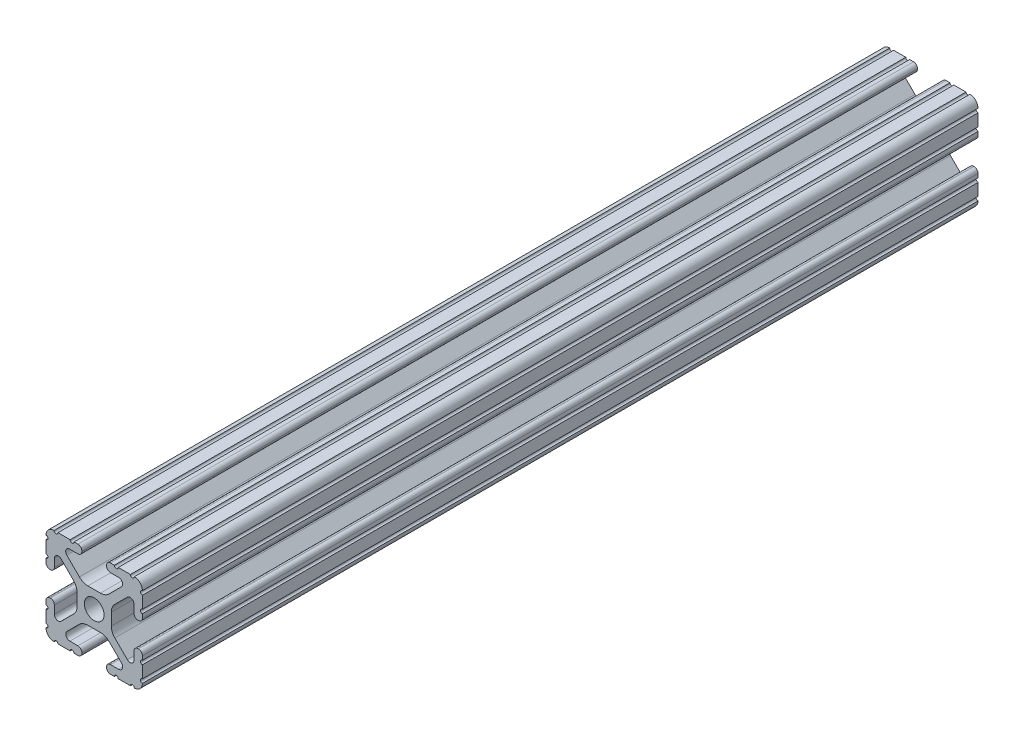
SolidWorks part; units mm, degrees
ref_plane "Front Plane" through (0, 0, 0) normal (0, 0, 1) x (1, 0, 0)
ref_plane "Top Plane" through (0, 0, 0) normal (0, 1, 0) x (1, 0, 0)
ref_plane "Right Plane" through (0, 0, 0) normal (1, 0, 0) x (0, 0, -1)
sketch "Sketch1" plane through (0, 0, 0) normal (0, 0, 1) x (1, 0, 0)
  line L88 (-7.1797, -8.6452) -> (-3.9523, -5.4237)
  line L89 (-1.7093, -4.4958) -> (1.7093, -4.4958)
  line L90 (3.9523, -5.4237) -> (7.1797, -8.6452)
  line L91 (6.4164, -10.4902) -> (4.2875, -10.4902)
  line L92 (3.2385, -11.5392) -> (3.2385, -11.651)
  line L93 (4.2875, -12.7) -> (5.3171, -12.7)
  line L94 (6.3331, -12.7) -> (9.5504, -12.7)
  line L95 (12.7, -9.5504) -> (12.7, -6.3331)
  line L96 (12.7, -5.3171) -> (12.7, -4.2875)
  line L97 (11.651, -3.2385) -> (11.5392, -3.2385)
  line L98 (10.4902, -4.2875) -> (10.4902, -6.4021)
  line L99 (8.7371, -7.1294) -> (5.441, -3.8408)
  line L100 (4.5085, -1.5932) -> (4.5085, 1.5932)
  line L101 (5.441, 3.8408) -> (8.7371, 7.1294)
  line L102 (10.4902, 6.4021) -> (10.4902, 4.2875)
  line L103 (11.5392, 3.2385) -> (11.651, 3.2385)
  line L104 (12.7, 4.2875) -> (12.7, 5.3171)
  line L105 (12.7, 6.3331) -> (12.7, 9.5504)
  line L106 (9.5504, 12.7) -> (6.3331, 12.7)
  line L107 (5.3171, 12.7) -> (4.2875, 12.7)
  line L108 (3.2385, 11.651) -> (3.2385, 11.5392)
  line L109 (4.2875, 10.4902) -> (6.4768, 10.4902)
  line L110 (7.207, 8.7244) -> (3.8983, 5.4232)
  line L111 (1.6558, 4.4958) -> (-1.6558, 4.4958)
  line L112 (-3.8983, 5.4232) -> (-7.207, 8.7244)
  line L113 (-6.4768, 10.4902) -> (-4.2875, 10.4902)
  line L114 (-3.2385, 11.5392) -> (-3.2385, 11.651)
  line L115 (-4.2875, 12.7) -> (-5.3171, 12.7)
  line L116 (-6.3331, 12.7) -> (-9.5504, 12.7)
  line L117 (-12.7, 9.5504) -> (-12.7, 6.3331)
  line L118 (-12.7, 5.3171) -> (-12.7, 4.2875)
  line L119 (-11.651, 3.2385) -> (-11.5392, 3.2385)
  line L120 (-10.4902, 4.2875) -> (-10.4902, 6.4021)
  line L121 (-8.7371, 7.1294) -> (-5.441, 3.8408)
  line L122 (-4.5085, 1.5932) -> (-4.5085, -1.5932)
  line L123 (-5.441, -3.8408) -> (-8.7371, -7.1294)
  line L124 (-10.4902, -6.4021) -> (-10.4902, -4.2875)
  line L125 (-11.5392, -3.2385) -> (-11.651, -3.2385)
  line L126 (-12.7, -4.2875) -> (-12.7, -5.3171)
  line L127 (-12.7, -6.3331) -> (-12.7, -9.5504)
  line L128 (-9.5504, -12.7) -> (-6.3331, -12.7)
  line L129 (-5.3171, -12.7) -> (-4.2875, -12.7)
  line L130 (-3.2385, -11.651) -> (-3.2385, -11.5392)
  line L131 (-4.2875, -10.4902) -> (-6.4164, -10.4902)
  circle A1 centre (0, 0) radius 2.6035
  arc A104 (-7.1797, -8.6452) -> (-6.4164, -10.4902) centre (-6.4164, -9.4098) ccw
  arc A105 (-1.7093, -4.4958) -> (-3.9523, -5.4237) centre (-1.7093, -7.6708) ccw
  arc A106 (3.9523, -5.4237) -> (1.7093, -4.4958) centre (1.7093, -7.6708) ccw
  arc A107 (6.4164, -10.4902) -> (7.1797, -8.6452) centre (6.4164, -9.4098) ccw
  arc A108 (4.2875, -10.4902) -> (3.2385, -11.5392) centre (4.2875, -11.5392) ccw
  arc A109 (3.2385, -11.651) -> (4.2875, -12.7) centre (4.2875, -11.651) ccw
  arc A110 (6.3331, -12.7) -> (5.3171, -12.7) centre (5.8251, -12.7) ccw
  arc A111 (10.5664, -12.6998) -> (9.5504, -12.7) centre (10.0584, -12.7) ccw
  arc A112 (10.5664, -12.6998) -> (12.6998, -10.5664) centre (10.5918, -10.5918) ccw
  arc A113 (12.7, -9.5504) -> (12.6998, -10.5664) centre (12.7, -10.0584) ccw
  arc A114 (12.7, -5.3171) -> (12.7, -6.3331) centre (12.7, -5.8251) ccw
  arc A115 (12.7, -4.2875) -> (11.651, -3.2385) centre (11.651, -4.2875) ccw
  arc A116 (11.5392, -3.2385) -> (10.4902, -4.2875) centre (11.5392, -4.2875) ccw
  arc A117 (8.7371, -7.1294) -> (10.4902, -6.4021) centre (9.4628, -6.4021) ccw
  arc A118 (4.5085, -1.5932) -> (5.441, -3.8408) centre (7.6835, -1.5932) ccw
  arc A119 (5.441, 3.8408) -> (4.5085, 1.5932) centre (7.6835, 1.5932) ccw
  arc A120 (10.4902, 6.4021) -> (8.7371, 7.1294) centre (9.4628, 6.4021) ccw
  arc A121 (10.4902, 4.2875) -> (11.5392, 3.2385) centre (11.5392, 4.2875) ccw
  arc A122 (11.651, 3.2385) -> (12.7, 4.2875) centre (11.651, 4.2875) ccw
  arc A123 (12.7, 6.3331) -> (12.7, 5.3171) centre (12.7, 5.8251) ccw
  arc A124 (12.6998, 10.5664) -> (12.7, 9.5504) centre (12.7, 10.0584) ccw
  arc A125 (12.6998, 10.5664) -> (10.5664, 12.6998) centre (10.5918, 10.5918) ccw
  arc A126 (9.5504, 12.7) -> (10.5664, 12.6998) centre (10.0584, 12.7) ccw
  arc A127 (5.3171, 12.7) -> (6.3331, 12.7) centre (5.8251, 12.7) ccw
  arc A128 (4.2875, 12.7) -> (3.2385, 11.651) centre (4.2875, 11.651) ccw
  arc A129 (3.2385, 11.5392) -> (4.2875, 10.4902) centre (4.2875, 11.5392) ccw
  arc A130 (7.207, 8.7244) -> (6.4768, 10.4902) centre (6.4768, 9.4563) ccw
  arc A131 (1.6558, 4.4958) -> (3.8983, 5.4232) centre (1.6558, 7.6708) ccw
  arc A132 (-3.8983, 5.4232) -> (-1.6558, 4.4958) centre (-1.6558, 7.6708) ccw
  arc A133 (-6.4768, 10.4902) -> (-7.207, 8.7244) centre (-6.4768, 9.4563) ccw
  arc A134 (-4.2875, 10.4902) -> (-3.2385, 11.5392) centre (-4.2875, 11.5392) ccw
  arc A135 (-3.2385, 11.651) -> (-4.2875, 12.7) centre (-4.2875, 11.651) ccw
  arc A136 (-6.3331, 12.7) -> (-5.3171, 12.7) centre (-5.8251, 12.7) ccw
  arc A137 (-10.5664, 12.6998) -> (-9.5504, 12.7) centre (-10.0584, 12.7) ccw
  arc A138 (-10.5664, 12.6998) -> (-12.6998, 10.5664) centre (-10.5918, 10.5918) ccw
  arc A139 (-12.7, 9.5504) -> (-12.6998, 10.5664) centre (-12.7, 10.0584) ccw
  arc A140 (-12.7, 5.3171) -> (-12.7, 6.3331) centre (-12.7, 5.8251) ccw
  arc A141 (-12.7, 4.2875) -> (-11.651, 3.2385) centre (-11.651, 4.2875) ccw
  arc A142 (-11.5392, 3.2385) -> (-10.4902, 4.2875) centre (-11.5392, 4.2875) ccw
  arc A143 (-8.7371, 7.1294) -> (-10.4902, 6.4021) centre (-9.4628, 6.4021) ccw
  arc A144 (-4.5085, 1.5932) -> (-5.441, 3.8408) centre (-7.6835, 1.5932) ccw
  arc A145 (-5.441, -3.8408) -> (-4.5085, -1.5932) centre (-7.6835, -1.5932) ccw
  arc A146 (-10.4902, -6.4021) -> (-8.7371, -7.1294) centre (-9.4628, -6.4021) ccw
  arc A147 (-10.4902, -4.2875) -> (-11.5392, -3.2385) centre (-11.5392, -4.2875) ccw
  arc A148 (-11.651, -3.2385) -> (-12.7, -4.2875) centre (-11.651, -4.2875) ccw
  arc A149 (-12.7, -6.3331) -> (-12.7, -5.3171) centre (-12.7, -5.8251) ccw
  arc A150 (-12.6998, -10.5664) -> (-12.7, -9.5504) centre (-12.7, -10.0584) ccw
  arc A151 (-12.6998, -10.5664) -> (-10.5664, -12.6998) centre (-10.5918, -10.5918) ccw
  arc A152 (-9.5504, -12.7) -> (-10.5664, -12.6998) centre (-10.0584, -12.7) ccw
  arc A153 (-5.3171, -12.7) -> (-6.3331, -12.7) centre (-5.8251, -12.7) ccw
  arc A154 (-4.2875, -12.7) -> (-3.2385, -11.651) centre (-4.2875, -11.651) ccw
  arc A155 (-3.2385, -11.5392) -> (-4.2875, -10.4902) centre (-4.2875, -11.5392) ccw
extrude "Boss-Extrude1" add sketch "Sketch1" along normal mid plane 609.6
sketch "Sketch2" plane through (12.7, 0, 0) normal (1, 0, 0) x (0, 0, -1)
  line L0 (-124.8229, -168.9819) -> (-124.8229, 45.4037) construction
  line L1 (-84.5663, -14.4703) -> (-84.5663, 14.7773)
  line L2 (-84.5663, 14.7773) -> (308.7706, 14.7773)
  line L3 (308.7706, 14.7773) -> (308.7706, -14.4703)
  line L4 (308.7706, -14.4703) -> (-84.5663, -14.4703)
extrude "Cut-Extrude1" cut sketch "Sketch2" against normal blind 29.21 and the other way blind 6.35
